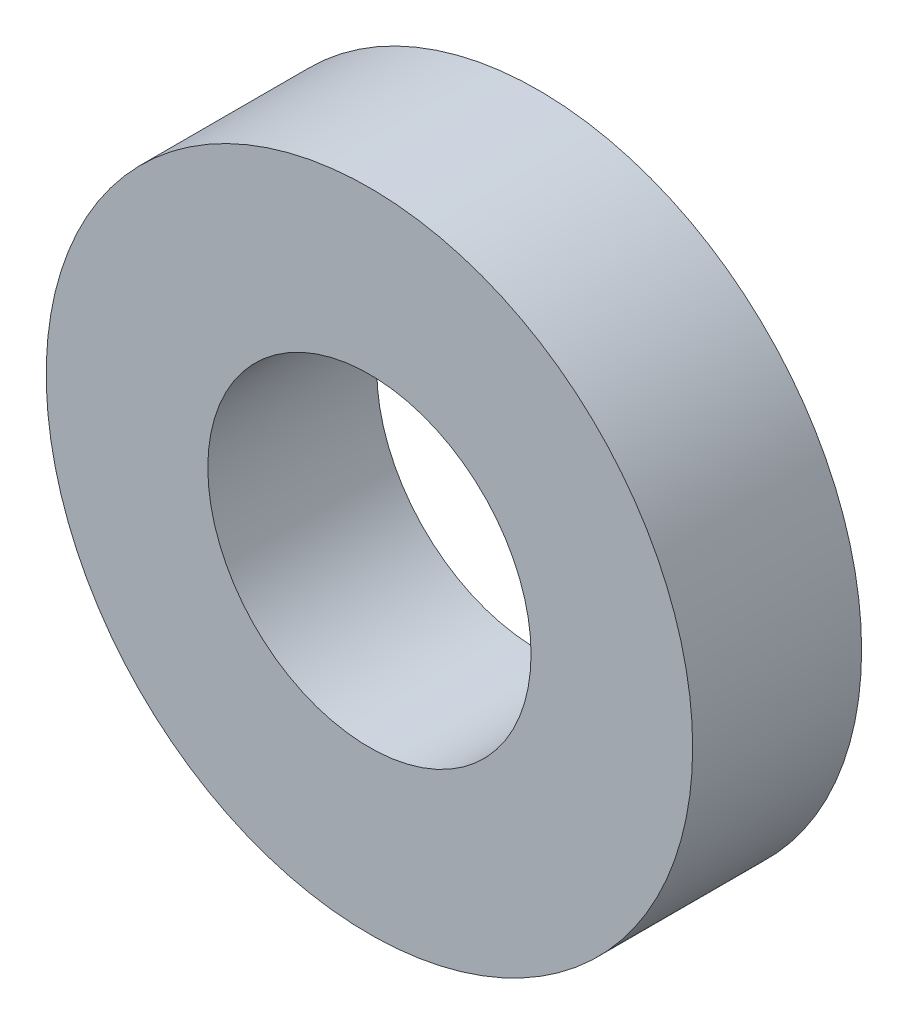
SolidWorks part; units mm, degrees
material "Cast Alloy Steel"
ref_plane "Front Plane" through (0, 0, 0) normal (0, 0, 1) x (1, 0, 0)
ref_plane "Top Plane" through (0, 0, 0) normal (0, 1, 0) x (1, 0, 0)
ref_plane "Right Plane" through (0, 0, 0) normal (1, 0, 0) x (0, 0, -1)
sketch "Sketch1" plane through (0, 0, 0) normal (0, 0, 1) x (1, 0, 0)
  circle A0 centre (0, 0) radius 4.7625
  circle A1 centre (0, 0) radius 9.525
  dimension "D1" = 9.525
  dimension "D2" = 19.05
extrude "Boss-Extrude1" add sketch "Sketch1" along normal blind 4.9784
